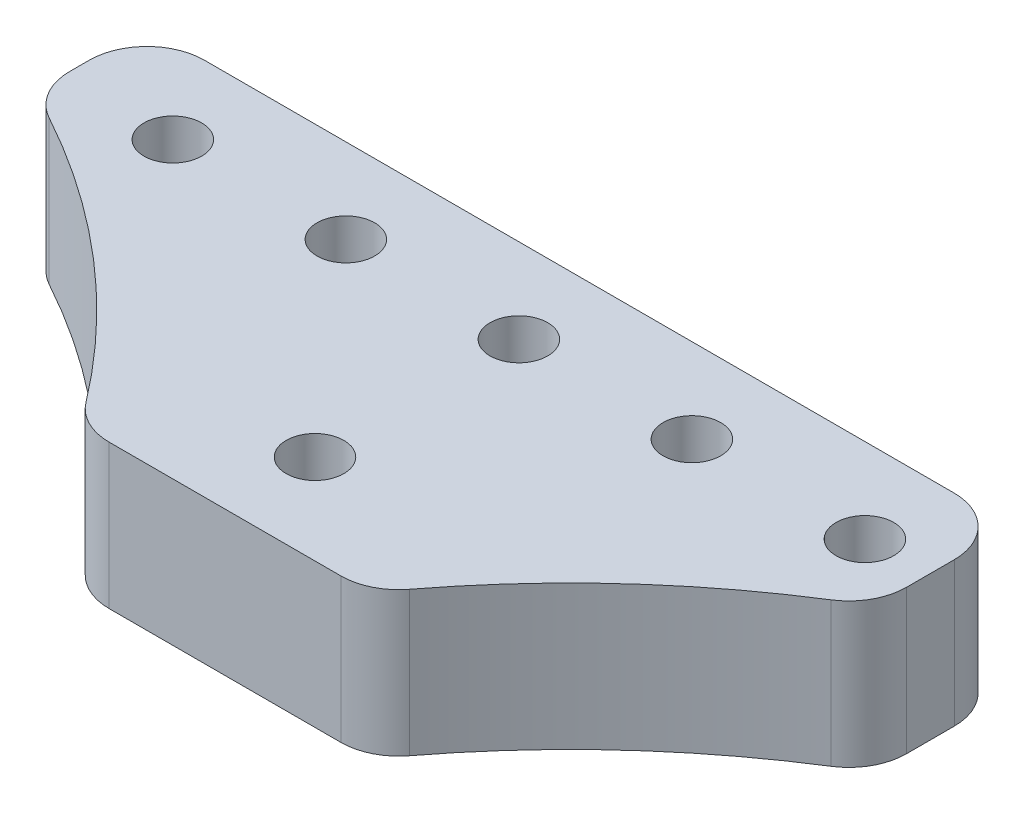
SolidWorks part; units mm, degrees
ref_plane "Front Plane" through (0, 0, 0) normal (0, 0, 1) x (1, 0, 0)
ref_plane "Top Plane" through (0, 0, 0) normal (0, 1, 0) x (1, 0, 0)
ref_plane "Right Plane" through (0, 0, 0) normal (1, 0, 0) x (0, 0, -1)
sketch "Sketch1" plane through (0, 0, 0) normal (0, 1, 0) x (1, 0, 0)
  line L0 (7.62, 0) -> (45.72, 0)
  line L1 (0, 0) -> (38.1, 0)
  line L2 (0, 0) -> (0, -25.4)
  line L3 (0, -25.4) -> (38.1, -25.4)
  line L4 (38.1, 0) -> (38.1, -25.4)
  line L5 (15.24, 0) -> (53.34, 0)
  line L6 (22.86, 0) -> (60.96, 0)
  line L7 (30.48, 0) -> (68.58, 0)
  line L8 (0, -12.7) -> (38.1, -12.7)
  line L9 (20.1062, -3.7209) -> (20.1062, -12.7)
  line L11 (0, 0) -> (38.1, 0)
  line L12 (0, 0) -> (0, -16.6652)
  line L13 (0, -16.6652) -> (38.1, -16.6652)
  line L14 (38.1, 0) -> (38.1, -16.6652)
  circle A0 centre (4.8662, -3.7209) radius 1.27
  circle A1 centre (12.4862, -3.7209) radius 1.27
  circle A2 centre (20.1062, -3.7209) radius 1.27
  circle A3 centre (27.7262, -3.7209) radius 1.27
  circle A4 centre (35.3462, -3.7209) radius 1.27
  circle A5 centre (20.1062, -12.7) radius 1.27
  arc A6 (13.7172, -16.6652) -> (0, -4.9311) centre (-16.431, -38.0238) ccw
  arc A7 (26.4952, -16.6652) -> (40.2125, -4.9311) centre (56.6434, -38.0238) cw
  point P35 (4.8662, -3.7209)
  point P36 (0, 0)
  dimension "D1" = 5
extrude "Boss-Extrude1" add sketch "Sketch1" along normal blind 6.35
fillet "Fillet1" radius 2.54 6 edges at (13.7172, 3.175, 16.6652) (26.4952, 3.175, 16.6652) (38.1, 3.175, 6.0669) (38.1, 3.175, 0) (0, 3.175, 0) (0, 3.175, 4.9311)
